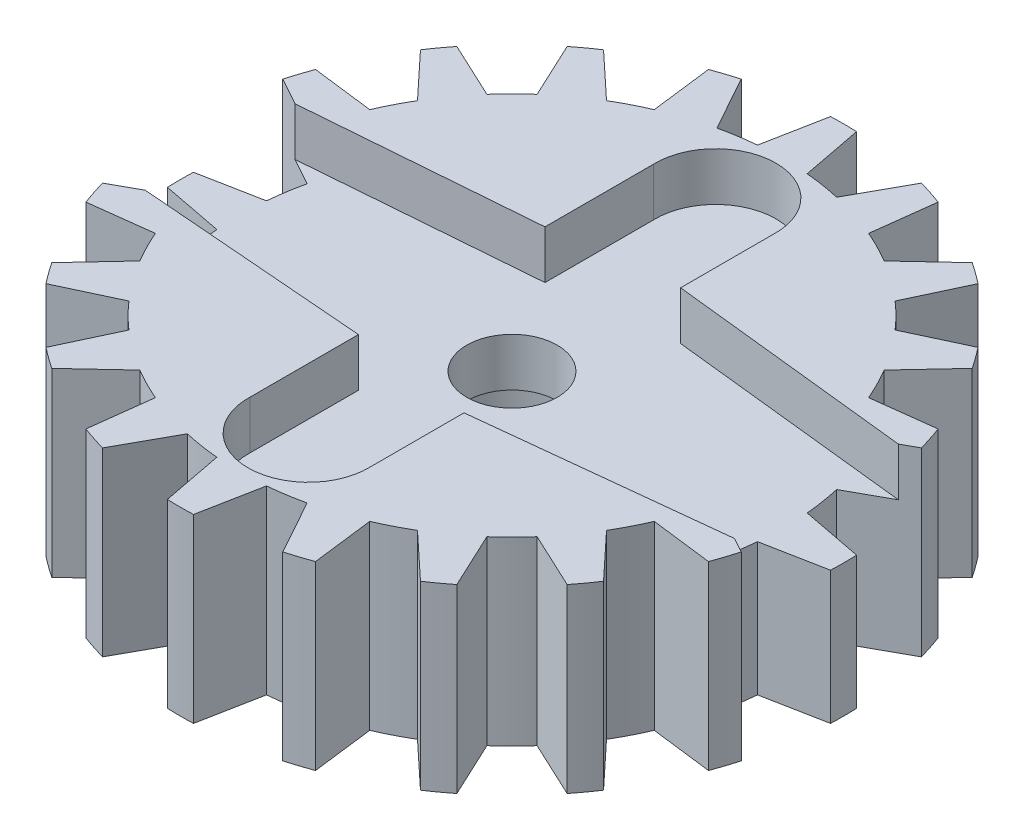
SolidWorks part; units mm, degrees
material "PBT General Purpose"
ref_plane "Front Plane" through (0, 0, 0) normal (0, 0, 1) x (1, 0, 0)
ref_plane "Top Plane" through (0, 0, 0) normal (0, 1, 0) x (1, 0, 0)
ref_plane "Right Plane" through (0, 0, 0) normal (1, 0, 0) x (0, 0, -1)
sketch "Sketch1" plane through (0, 0, 0) normal (0, 1, 0) x (1, 0, 0)
  circle A0 centre (0, 0) radius 1.5
  circle A1 centre (0, 0) radius 11
  dimension "D1" = 3
  dimension "D2" = 22
extrude "Boss-Extrude1" add sketch "Sketch1" along normal blind 6
sketch "Sketch2" plane through (0, 6, 0) normal (0, 1, 0) x (1, 0, 0)
  line L0 (0, 0) -> (0, 15.5) construction
  line L1 (0, 0) -> (-0.4319, 10.9915) construction
  line L2 (0, 0) -> (-0.8235, 8.9622) construction
  line L3 (0, 0) -> (-1.4079, 8.8892) construction
  line L4 (-0.8235, 8.9622) -> (-0.4319, 10.9915)
  line L5 (0.8235, 8.9622) -> (0.4319, 10.9915)
  line L6 (-1.4079, 8.8892) -> (-2.6837, 16.9442)
  line L7 (-2.6837, 16.9442) -> (2.6837, 16.9442)
  line L8 (2.6837, 16.9442) -> (1.4079, 8.8892)
  circle A0 centre (0, 0) radius 11 construction
  arc A1 (0.4319, 10.9915) -> (-0.4319, 10.9915) centre (0, 0) ccw
  arc A3 (-0.8235, 8.9622) -> (-1.4079, 8.8892) centre (0, 0) ccw
  arc A4 (0.8235, 8.9622) -> (1.4079, 8.8892) centre (0, 0) cw
  dimension "D4" = 9
  dimension "D1" = 2.25
  dimension "D2" = 3
  dimension "D3" = 3.75
extrude "Cut-Extrude1" cut sketch "Sketch2" against normal up to next (6 mm away)
pattern_circular "CirPattern1" count 20 over 360 about axis through (0, 0, 0) along (0, 1, 0) of "Cut-Extrude1"
sketch "Sketch3" plane through (0, 6, 0) normal (0, 1, 0) x (1, 0, 0)
  line L0 (15.75, 0) -> (-15.75, 0) construction
  line L1 (0, -6.75) -> (0, 6.75) construction
  line L2 (-1.8988, 6.6833) -> (-1.8988, 3) construction
  line L3 (1.8988, 6.6833) -> (1.8988, 3.5) construction
  line L4 (-15.75, 1.9) -> (-1.8988, 3) construction
  line L5 (15.7506, 2) -> (1.8988, 3.5) construction
  line L6 (15.7506, -2) -> (1.8988, -3.5) construction
  line L7 (1.8988, -6.6833) -> (1.8988, -3.5) construction
  line L8 (-1.8988, -6.6833) -> (-1.8988, -3) construction
  line L9 (-15.75, -1.9) -> (-1.8988, -3) construction
  line L10 (-1.9988, 6.6816) -> (-1.9988, 3.0924)
  line L11 (-15.754, 2) -> (-1.9988, 3.0924)
  line L12 (-15.754, -2) -> (-1.9988, -3.0924)
  line L13 (-1.9988, -6.6816) -> (-1.9988, -3.0924)
  line L14 (1.9988, -6.6816) -> (1.9988, -3.5898)
  line L15 (15.7561, -2.1) -> (1.9988, -3.5898)
  line L16 (15.7561, 2.1) -> (1.9988, 3.5898)
  line L17 (1.9988, 6.6816) -> (1.9988, 3.5898)
  line L18 (-12, 2.2981) -> (-12, -2.2981)
  line L19 (12, 2.5067) -> (12, -2.5067)
  circle A0 centre (0, 0) radius 1.25
  arc A1 (-1.8988, 6.6833) -> (1.8988, 6.6833) centre (0, 6.75) cw construction
  arc A2 (-15.75, 1.9) -> (-15.75, -1.9) centre (-15.75, 0) ccw construction
  arc A3 (15.7506, 2) -> (15.7506, -2) centre (15.75, 0) cw construction
  arc A4 (-1.8988, -6.6833) -> (1.8988, -6.6833) centre (0, -6.75) ccw construction
  arc A5 (-15.754, 2) -> (-15.754, -2) centre (-15.75, 0) ccw
  arc A6 (-1.9988, -6.6816) -> (1.9988, -6.6816) centre (0, -6.75) ccw
  arc A7 (15.7561, 2.1) -> (15.7561, -2.1) centre (15.75, 0) cw
  arc A8 (-1.9988, 6.6816) -> (1.9988, 6.6816) centre (0, 6.75) cw
  point P5 (0, 0)
  point P8 (0, 0)
  dimension "D1" = 2.5
  dimension "D4" = 1.9
  dimension "D5" = 1.9
  dimension "D11" = 2
  dimension "D2" = 13.5
  dimension "D3" = 31.5
  dimension "D6" = 1.1
  dimension "D8" = 6
  dimension "D9" = 7
  dimension "D10" = 3.5
  dimension "D12" = 12
  dimension "D13" = 12
  dimension "D7" = 0.1
extrude "Cut-Extrude2" cut sketch "Sketch3" against normal blind 1.6 contours A8 L10 L11 A5 L12 L13 A6 L14 L15 A7 L16 L17 A4 L8 L9 A2 L4 L2 A1 L3 L5 A3 L6 L7 | L8 A4 L7 L6 A3 L5 L3 A1 L2 L4 A2 L9 A0
sketch "Sketch4" plane through (0, 0, 0) normal (0, -1, 0) x (1, 0, 0)
  circle A0 centre (0, 0) radius 2.6
  dimension "D1" = 5.2
extrude "Cut-Extrude3" cut sketch "Sketch4" against normal offset from surface (2.8 mm away) 1.6 up to face at (0, 4.4, 1.5)
equation "\"num_teeth\"= 20"
equation "\"D1@Sketch2\"=(1.5/6)*(360 / \"num_teeth\")*0.5"
equation "\"D2@Sketch2\"=(2/6)*(360 / \"num_teeth\")*0.5"
equation "\"D3@Sketch2\"=(2.5/6)*(360 / \"num_teeth\")*0.5"
equation "\"D1@CirPattern1\"=\"num_teeth\""
equation "\"diameter\" = 20mm"
equation "\"D2@Sketch1\"=\"diameter\" + 2"
equation "\"D4@Sketch2\"=(\"diameter\" / 2) - 1"
